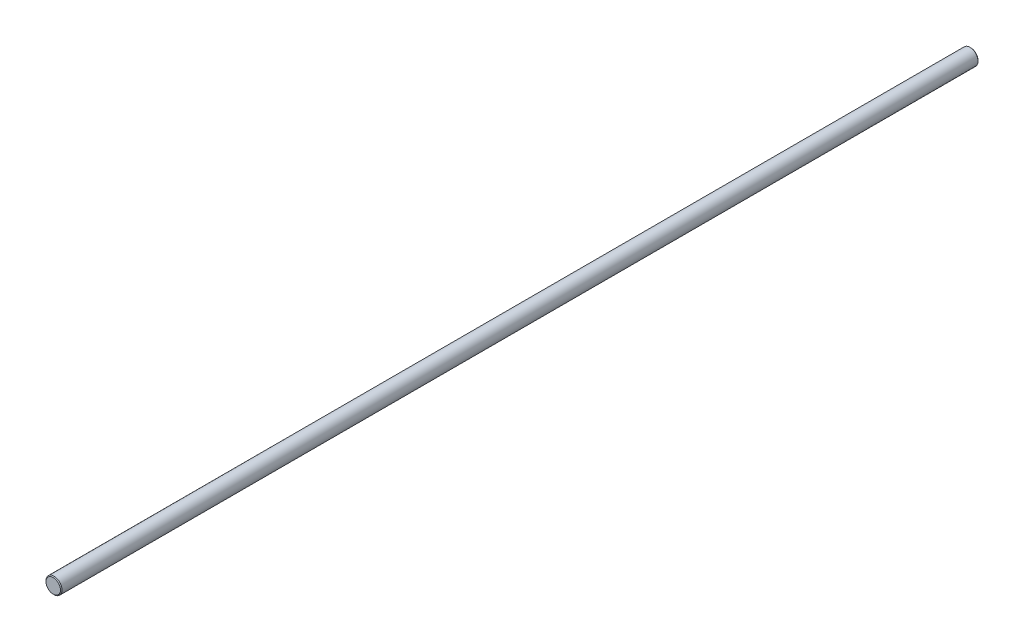
SolidWorks part; units mm, degrees
ref_plane "Front Plane" through (0, 0, 0) normal (0, 0, 1) x (1, 0, 0)
ref_plane "Top Plane" through (0, 0, 0) normal (0, 1, 0) x (1, 0, 0)
ref_plane "Right Plane" through (0, 0, 0) normal (1, 0, 0) x (0, 0, -1)
sketch "Sketch1" plane through (0, 0, 0) normal (0, 0, 1) x (1, 0, 0)
  circle A0 centre (0, 0) radius 4
  dimension "D1" = 8
extrude "Extrude1" add sketch "Sketch1" along normal mid plane 457.2
ref_plane "Plane1" through (0, 4, 0) normal (0, 1, 0) x (1, 0, 0)
chamfer "Chamfer1" distance 0.4 angle 45 2 edges at (4, 0, -228.6) (4, 0, 228.6)
sketch "Sketch2" plane through (0, 0, 228.6) normal (0, 0, 1) x (1, 0, 0)
